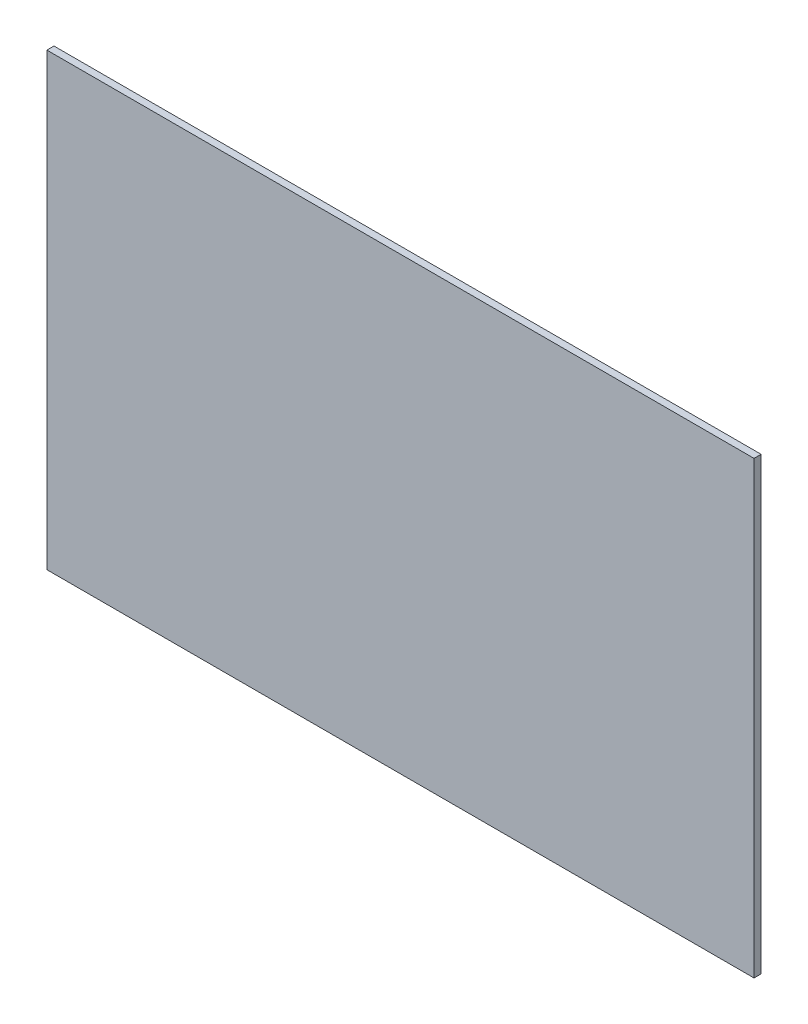
SolidWorks part; units mm, degrees
ref_plane "Front Plane" through (0, 0, 0) normal (0, 0, 1) x (1, 0, 0)
ref_plane "Top Plane" through (0, 0, 0) normal (0, 1, 0) x (1, 0, 0)
ref_plane "Right Plane" through (0, 0, 0) normal (1, 0, 0) x (0, 0, -1)
sketch "Sketch1" plane through (0, 0, 0) normal (0, 0, 1) x (1, 0, 0)
  line L1 (-139.7, -88.9) -> (139.7, -88.9)
  line L2 (-139.7, -88.9) -> (-139.7, 88.9)
  line L3 (-139.7, 88.9) -> (139.7, 88.9)
  line L4 (139.7, -88.9) -> (139.7, 88.9)
  line L5 (-139.7, -88.9) -> (139.7, 88.9) construction
  line L6 (-139.7, 88.9) -> (139.7, -88.9) construction
  point P0 (0, 0)
  dimension "D1" = 279.4
  dimension "D2" = 177.8
extrude "Boss-Extrude1" add sketch "Sketch1" along normal blind 2.794
